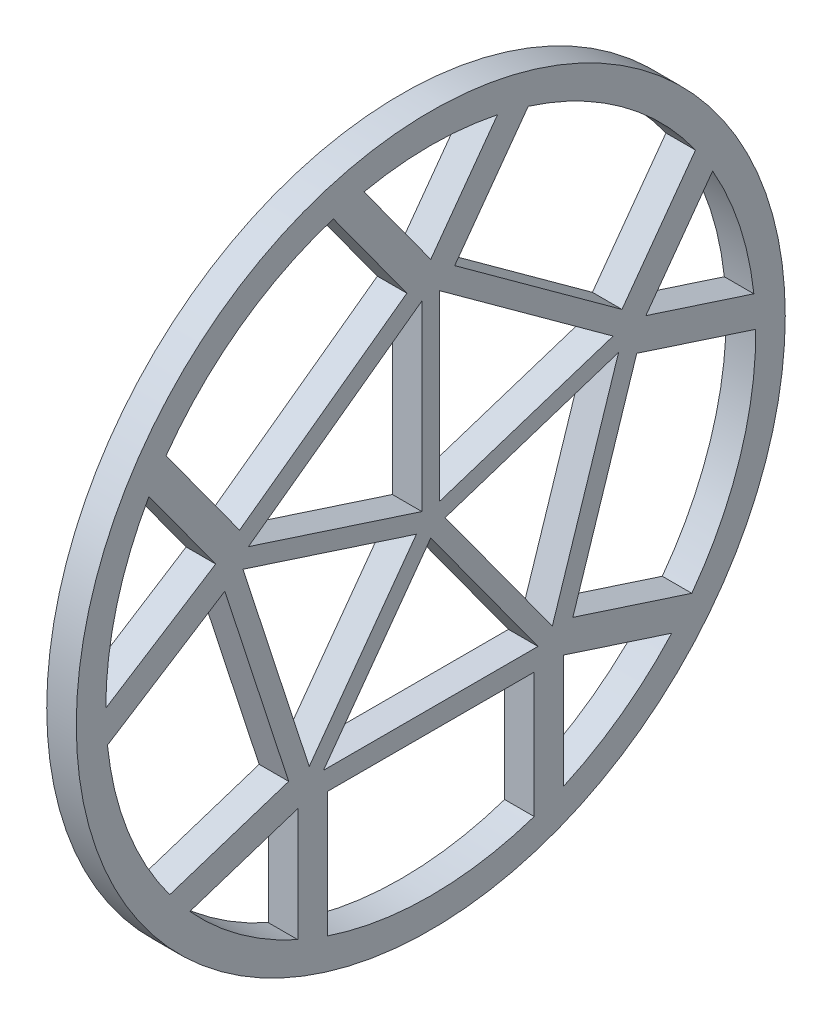
SolidWorks part; units mm, degrees
ref_plane "Front Plane" through (0, 0, 0) normal (0, 0, 1) x (1, 0, 0)
ref_plane "Top Plane" through (0, 0, 0) normal (0, 1, 0) x (1, 0, 0)
ref_plane "Right Plane" through (0, 0, 0) normal (1, 0, 0) x (0, 0, -1)
sketch "Sketch2" plane through (0, 0, 0) normal (1, 0, 0) x (0, 0, -1)
  line L83 (-36.4058, 11.829) -> (-22.5, -30.9686)
  line L84 (-22.5, -30.9686) -> (22.5, -30.9686)
  line L85 (22.5, -30.9686) -> (36.4058, 11.829)
  line L86 (36.4058, 11.829) -> (0, 38.2793)
  line L87 (0, 38.2793) -> (-36.4058, 11.829)
  line L110 (-36.4058, 11.829) -> (-47.7021, 27.3771)
  line L111 (-36.4058, 11.829) -> (-55, 0)
  line L112 (-36.4058, 11.829) -> (-29.0348, 17.1843)
  line L113 (-36.4058, 11.829) -> (-32.3607, 14.7679)
  line L114 (-32.3607, 14.7679) -> (-44.8059, 31.8972)
  line L115 (-36.4058, 11.829) -> (-34.8607, 7.0737)
  line L116 (-34.8607, 7.0737) -> (-54.7183, -5.559)
  line L117 (-22.5, -30.9686) -> (-22.5, -50.1871)
  line L118 (-1.3724, 30.9382) -> (1.3724, 30.9382)
  line L119 (-22.5, -30.9686) -> (-40.7779, -36.9075)
  line L120 (-22.5, -30.9686) -> (-17.5, -30.9686)
  line L121 (-17.5, -30.9686) -> (-17.5, -52.1416)
  line L122 (-22.5, -30.9686) -> (-24.0451, -26.2133)
  line L123 (-24.0451, -26.2133) -> (-44.1818, -32.7561)
  line L124 (22.5, -30.9686) -> (22.5, -50.1871)
  line L125 (22.5, -30.9686) -> (40.7779, -36.9075)
  line L126 (22.5, -30.9686) -> (17.5, -30.9686)
  line L127 (17.5, -30.9686) -> (17.5, -52.1416)
  line L128 (22.5, -30.9686) -> (24.0451, -26.2133)
  line L129 (24.0451, -26.2133) -> (44.1818, -32.7561)
  line L130 (36.4058, 11.829) -> (47.7021, 27.3771)
  line L131 (36.4058, 11.829) -> (54.6837, 5.8901)
  line L132 (36.4058, 11.829) -> (32.3607, 14.7679)
  line L133 (32.3607, 14.7679) -> (46.1239, 33.7114)
  line L134 (36.4058, 11.829) -> (34.8607, 7.0737)
  line L135 (34.8607, 7.0737) -> (54.9974, 0.5308)
  line L136 (0, 38.2793) -> (-11.2964, 53.8274)
  line L137 (0, 38.2793) -> (11.2964, 53.8274)
  line L138 (0, 38.2793) -> (-4.0451, 35.3404)
  line L139 (-4.0451, 35.3404) -> (-16.4903, 52.4697)
  line L140 (0, 38.2793) -> (4.0451, 35.3404)
  line L141 (4.0451, 35.3404) -> (16.4903, 52.4697)
  line L142 (0, 0) -> (32.3607, 10.5146) construction
  line L143 (-32.3607, 10.5146) -> (-20, -27.5276)
  line L144 (-20, -27.5276) -> (20, -27.5276)
  line L145 (20, -27.5276) -> (32.3607, 10.5146)
  line L146 (32.3607, 10.5146) -> (0, 34.026)
  line L147 (0, 34.026) -> (-32.3607, 10.5146)
  line L148 (0, 0) -> (0, 34.026) construction
  line L149 (0, 0) -> (-32.3607, 10.5146) construction
  line L150 (0, 0) -> (-20, -27.5276) construction
  line L151 (0, 0) -> (20, -27.5276) construction
  line L152 (0, 1.5772) -> (30.8607, 11.6044)
  line L153 (0.9271, -1.276) -> (31.7877, 8.7513)
  line L154 (-30.8607, 11.6044) -> (0, 1.5772)
  line L155 (-31.7877, 8.7513) -> (-0.9271, -1.276)
  line L156 (-20.5729, -25.7643) -> (-2.4271, -0.7886)
  line L157 (-18.1459, -27.5276) -> (0.9271, -1.276)
  line L158 (18.1459, -27.5276) -> (0, -2.552)
  line L159 (20.5729, -25.7643) -> (2.4271, -0.7886)
  line L160 (-1.5, 32.9362) -> (-1.5, 2.0646)
  line L161 (1.5, 32.9362) -> (1.5, 2.0646)
  line L162 (-36.4058, 11.829) -> (-55, 0)
  circle A0 centre (0, 0) radius 60
  circle A1 centre (0, 0) radius 55
  circle A2 centre (0, 0) radius 30.9686 construction
  circle A3 centre (0, 0) radius 27.5276 construction
  dimension "D1" = 120
  dimension "D2" = 110
  dimension "D3" = 45
  dimension "D4" = 5
  dimension "D5" = 5
  dimension "D6" = 5
  dimension "D7" = 5
  dimension "D8" = 5
  dimension "D9" = 5
  dimension "D10" = 72
  dimension "D11" = 5
  dimension "D12" = 5
  dimension "D13" = 5
  dimension "D14" = 5
  dimension "D15" = 72
  dimension "D16" = 40
  dimension "D17" = 3
  dimension "D18" = 3
  dimension "D19" = 3
  dimension "D20" = 3
  dimension "D21" = 3
  dimension "D22" = 1.5
  dimension "D23" = 1.5
  dimension "D24" = 1.5
extrude "Boss-Extrude2" add sketch "Sketch2" along normal blind 5
